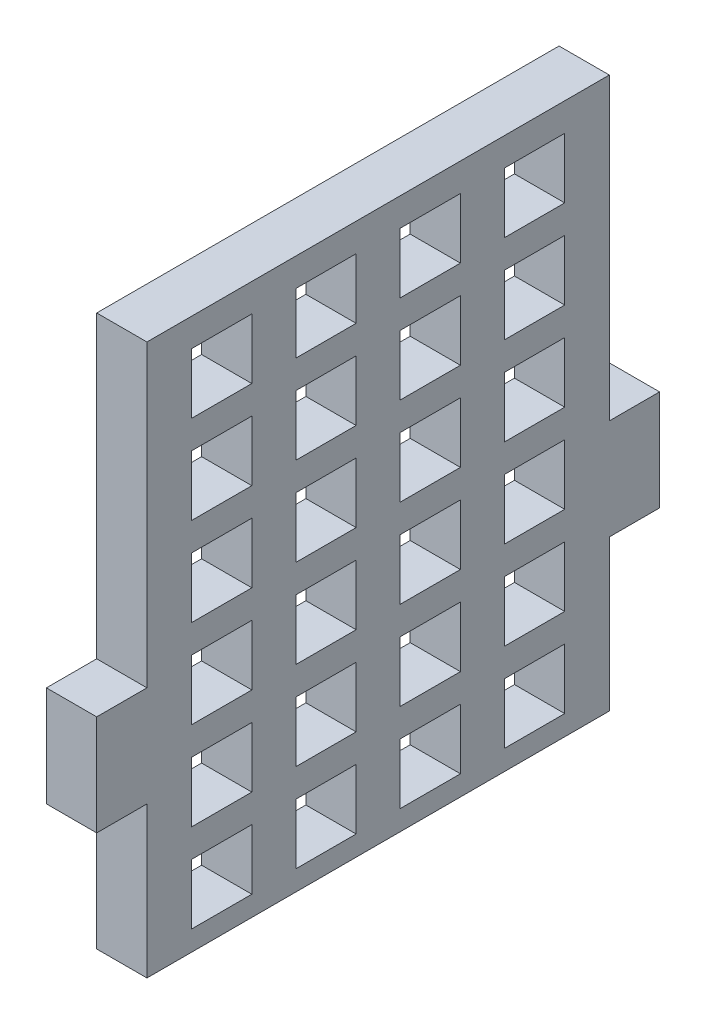
SolidWorks part; units mm, degrees
ref_plane "Front Plane" through (0, 0, 0) normal (0, 0, 1) x (1, 0, 0)
ref_plane "Top Plane" through (0, 0, 0) normal (0, 1, 0) x (1, 0, 0)
ref_plane "Right Plane" through (0, 0, 0) normal (1, 0, 0) x (0, 0, -1)
sketch "Sketch1" plane through (0, 0, 0) normal (1, 0, 0) x (0, 0, -1)
  line L1 (0, 0) -> (35.56, 0)
  line L2 (0, 0) -> (0, 41.148)
  line L3 (0, 41.148) -> (35.56, 41.148)
  line L4 (35.56, 0) -> (35.56, 41.148)
  dimension "D1" = 41.148
  dimension "D2" = 35.56
extrude "Extrude1" add sketch "Sketch1" along normal blind 3.175
sketch "Sketch2" plane through (3.175, 0, 0) normal (1, 0, 0) x (0, 0, -1)
  line L0 (17.78, 41.148) -> (17.78, 0) construction
  line L1 (35.56, 41.148) -> (0, 41.148) construction
  line L2 (0, 0) -> (35.56, 0) construction
  line L4 (0, 41.148) -> (0, 0) construction
  line L6 (3.175, 41.148) -> (3.175, 22.225)
  line L7 (3.175, 22.225) -> (0, 22.225)
  line L8 (32.385, 22.225) -> (35.56, 22.225)
  line L9 (32.385, 41.148) -> (32.385, 22.225)
  line L10 (32.385, 0) -> (32.385, 15.875)
  line L11 (32.385, 15.875) -> (35.56, 15.875)
  line L12 (3.175, 15.875) -> (0, 15.875)
  line L13 (3.175, 0) -> (3.175, 15.875)
  line L14 (0, 22.225) -> (0, 41.148)
  line L15 (0, 41.148) -> (3.175, 41.148)
  line L16 (32.385, 41.148) -> (35.56, 41.148)
  line L17 (35.56, 41.148) -> (35.56, 22.225)
  line L18 (35.56, 15.875) -> (35.56, 0)
  line L19 (35.56, 0) -> (32.385, 0)
  line L20 (3.175, 0) -> (0, 0)
  line L21 (0, 0) -> (0, 15.875)
  dimension "D1" = 3.175
extrude "Cut-Extrude3" cut sketch "Sketch2" against normal through all
sketch "Sketch3" plane through (3.175, 0, 0) normal (1, 0, 0) x (0, 0, -1)
  line L0 (3.175, 0) -> (3.175, 15.875) construction
  line L1 (3.175, 6.35) -> (32.385, 6.35)
  line L2 (3.175, 6.35) -> (3.175, 0)
  line L3 (3.175, 0) -> (32.385, 0)
  line L4 (32.385, 6.35) -> (32.385, 0)
  dimension "D1" = 6.35
extrude "Cut-Extrude4" cut sketch "Sketch3" against normal through all
sketch "Sketch4" plane through (3.175, 0, 0) normal (1, 0, 0) x (0, 0, -1)
  line L0 (32.385, 41.148) -> (3.175, 41.148) construction
  line L1 (3.175, 41.148) -> (32.385, 41.148) construction
  line L2 (3.175, 41.148) -> (3.175, 6.35) construction
  line L3 (3.175, 6.35) -> (32.385, 6.35) construction
  line L4 (32.385, 41.148) -> (32.385, 6.35) construction
  line L8 (12.5806, 11.43) -> (16.3906, 11.43)
  line L9 (5.9917, 11.43) -> (9.8017, 11.43)
  line L10 (5.9917, 11.43) -> (5.9917, 7.62)
  line L11 (5.9917, 7.62) -> (9.8017, 7.62)
  line L12 (9.8017, 11.43) -> (9.8017, 7.62)
  line L13 (12.5806, 11.43) -> (12.5806, 7.62)
  line L14 (12.5806, 7.62) -> (16.3906, 7.62)
  line L15 (16.3906, 11.43) -> (16.3906, 7.62)
  line L16 (19.1694, 11.43) -> (22.9794, 11.43)
  line L17 (19.1694, 11.43) -> (19.1694, 7.62)
  line L18 (19.1694, 7.62) -> (22.9794, 7.62)
  line L19 (22.9794, 11.43) -> (22.9794, 7.62)
  line L20 (25.7583, 11.43) -> (29.5683, 11.43)
  line L21 (25.7583, 11.43) -> (25.7583, 7.62)
  line L22 (25.7583, 7.62) -> (29.5683, 7.62)
  line L23 (29.5683, 11.43) -> (29.5683, 7.62)
  line L24 (5.9917, 7.62) -> (29.5683, 7.62) construction
  line L25 (29.5683, 7.62) -> (29.7732, 7.7383) construction
  line L26 (12.5806, 17.018) -> (16.3906, 17.018)
  line L27 (5.9917, 17.018) -> (9.8017, 17.018)
  line L28 (5.9917, 17.018) -> (5.9917, 13.208)
  line L29 (5.9917, 13.208) -> (9.8017, 13.208)
  line L30 (9.8017, 17.018) -> (9.8017, 13.208)
  line L31 (12.5806, 17.018) -> (12.5806, 13.208)
  line L32 (12.5806, 13.208) -> (16.3906, 13.208)
  line L33 (16.3906, 17.018) -> (16.3906, 13.208)
  line L34 (19.1694, 17.018) -> (22.9794, 17.018)
  line L35 (19.1694, 17.018) -> (19.1694, 13.208)
  line L36 (19.1694, 13.208) -> (22.9794, 13.208)
  line L37 (22.9794, 17.018) -> (22.9794, 13.208)
  line L38 (25.7583, 17.018) -> (29.5683, 17.018)
  line L39 (25.7583, 17.018) -> (25.7583, 13.208)
  line L40 (25.7583, 13.208) -> (29.5683, 13.208)
  line L41 (29.5683, 17.018) -> (29.5683, 13.208)
  line L42 (3.175, 11.938) -> (32.385, 11.938) construction
  line L43 (5.9917, 13.208) -> (29.5683, 13.208) construction
  line L44 (29.5683, 13.208) -> (29.7732, 13.3263) construction
  line L45 (12.5806, 22.606) -> (16.3906, 22.606)
  line L46 (5.9917, 22.606) -> (9.8017, 22.606)
  line L47 (5.9917, 22.606) -> (5.9917, 18.796)
  line L48 (5.9917, 18.796) -> (9.8017, 18.796)
  line L49 (9.8017, 22.606) -> (9.8017, 18.796)
  line L50 (12.5806, 22.606) -> (12.5806, 18.796)
  line L51 (12.5806, 18.796) -> (16.3906, 18.796)
  line L52 (16.3906, 22.606) -> (16.3906, 18.796)
  line L53 (19.1694, 22.606) -> (22.9794, 22.606)
  line L54 (19.1694, 22.606) -> (19.1694, 18.796)
  line L55 (19.1694, 18.796) -> (22.9794, 18.796)
  line L56 (22.9794, 22.606) -> (22.9794, 18.796)
  line L57 (25.7583, 22.606) -> (29.5683, 22.606)
  line L58 (25.7583, 22.606) -> (25.7583, 18.796)
  line L59 (25.7583, 18.796) -> (29.5683, 18.796)
  line L60 (29.5683, 22.606) -> (29.5683, 18.796)
  line L61 (3.175, 17.526) -> (32.385, 17.526) construction
  line L62 (5.9917, 18.796) -> (29.5683, 18.796) construction
  line L63 (29.5683, 18.796) -> (29.7732, 18.9143) construction
  line L64 (12.5806, 28.194) -> (16.3906, 28.194)
  line L65 (5.9917, 28.194) -> (9.8017, 28.194)
  line L66 (5.9917, 28.194) -> (5.9917, 24.384)
  line L67 (5.9917, 24.384) -> (9.8017, 24.384)
  line L68 (9.8017, 28.194) -> (9.8017, 24.384)
  line L69 (12.5806, 28.194) -> (12.5806, 24.384)
  line L70 (12.5806, 24.384) -> (16.3906, 24.384)
  line L71 (16.3906, 28.194) -> (16.3906, 24.384)
  line L72 (19.1694, 28.194) -> (22.9794, 28.194)
  line L73 (19.1694, 28.194) -> (19.1694, 24.384)
  line L74 (19.1694, 24.384) -> (22.9794, 24.384)
  line L75 (22.9794, 28.194) -> (22.9794, 24.384)
  line L76 (25.7583, 28.194) -> (29.5683, 28.194)
  line L77 (25.7583, 28.194) -> (25.7583, 24.384)
  line L78 (25.7583, 24.384) -> (29.5683, 24.384)
  line L79 (29.5683, 28.194) -> (29.5683, 24.384)
  line L80 (3.175, 23.114) -> (32.385, 23.114) construction
  line L81 (5.9917, 24.384) -> (29.5683, 24.384) construction
  line L82 (29.5683, 24.384) -> (29.7732, 24.5023) construction
  line L83 (12.5806, 33.782) -> (16.3906, 33.782)
  line L84 (5.9917, 33.782) -> (9.8017, 33.782)
  line L85 (5.9917, 33.782) -> (5.9917, 29.972)
  line L86 (5.9917, 29.972) -> (9.8017, 29.972)
  line L87 (9.8017, 33.782) -> (9.8017, 29.972)
  line L88 (12.5806, 33.782) -> (12.5806, 29.972)
  line L89 (12.5806, 29.972) -> (16.3906, 29.972)
  line L90 (16.3906, 33.782) -> (16.3906, 29.972)
  line L91 (19.1694, 33.782) -> (22.9794, 33.782)
  line L92 (19.1694, 33.782) -> (19.1694, 29.972)
  line L93 (19.1694, 29.972) -> (22.9794, 29.972)
  line L94 (22.9794, 33.782) -> (22.9794, 29.972)
  line L95 (25.7583, 33.782) -> (29.5683, 33.782)
  line L96 (25.7583, 33.782) -> (25.7583, 29.972)
  line L97 (25.7583, 29.972) -> (29.5683, 29.972)
  line L98 (29.5683, 33.782) -> (29.5683, 29.972)
  line L99 (3.175, 28.702) -> (32.385, 28.702) construction
  line L100 (5.9917, 29.972) -> (29.5683, 29.972) construction
  line L101 (29.5683, 29.972) -> (29.7732, 30.0903) construction
  line L102 (12.5806, 39.37) -> (16.3906, 39.37)
  line L103 (5.9917, 39.37) -> (9.8017, 39.37)
  line L104 (5.9917, 39.37) -> (5.9917, 35.56)
  line L105 (5.9917, 35.56) -> (9.8017, 35.56)
  line L106 (9.8017, 39.37) -> (9.8017, 35.56)
  line L107 (12.5806, 39.37) -> (12.5806, 35.56)
  line L108 (12.5806, 35.56) -> (16.3906, 35.56)
  line L109 (16.3906, 39.37) -> (16.3906, 35.56)
  line L110 (19.1694, 39.37) -> (22.9794, 39.37)
  line L111 (19.1694, 39.37) -> (19.1694, 35.56)
  line L112 (19.1694, 35.56) -> (22.9794, 35.56)
  line L113 (22.9794, 39.37) -> (22.9794, 35.56)
  line L114 (25.7583, 39.37) -> (29.5683, 39.37)
  line L115 (25.7583, 39.37) -> (25.7583, 35.56)
  line L116 (25.7583, 35.56) -> (29.5683, 35.56)
  line L117 (29.5683, 39.37) -> (29.5683, 35.56)
  line L118 (3.175, 34.29) -> (32.385, 34.29) construction
  line L119 (5.9917, 35.56) -> (29.5683, 35.56) construction
  line L120 (29.5683, 35.56) -> (29.7732, 35.6783) construction
  dimension "D1" = 3.81
  dimension "D2" = 3.81
  dimension "D3" = 29.21
  dimension "D4" = 1.27
  dimension "D5" = 2.8167
  dimension "D6" = 2.8167
extrude "Cut-Extrude5" cut sketch "Sketch4" against normal through all
equation "\"D6@Sketch4\" = \"D5@Sketch4\""
